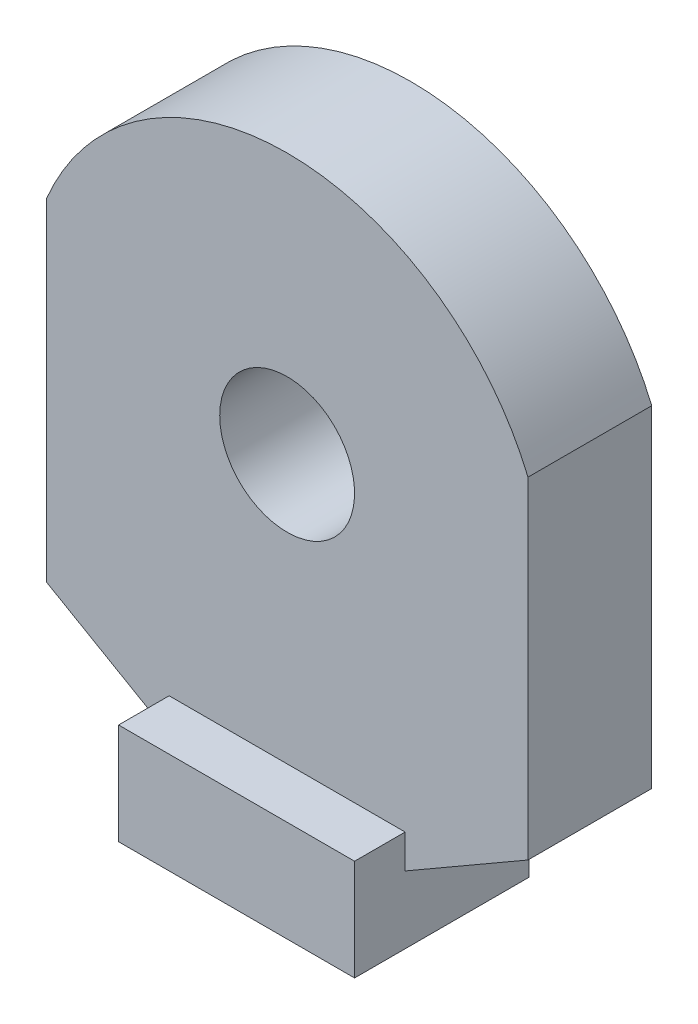
SolidWorks part; units mm, degrees
ref_plane "Plan de face" through (0, 0, 0) normal (0, 0, 1) x (1, 0, 0)
ref_plane "Plan de dessus" through (0, 0, 0) normal (0, 1, 0) x (1, 0, 0)
ref_plane "Plan de droite" through (0, 0, 0) normal (1, 0, 0) x (0, 0, -1)
sketch "Esquisse1" plane through (0, 0, 0) normal (0, 0, 1) x (1, 0, 0)
  line L0 (-14.29, -13.6911) -> (-14.29, 5.978)
  line L1 (-14.29, -13.6911) -> (-7, -17.9)
  line L2 (-7, -17.9) -> (-7, -21.9)
  line L3 (0, -21.9) -> (0, 14.503) construction
  line L4 (-7, -21.9) -> (7, -21.9)
  line L5 (7, -17.9) -> (7, -21.9)
  line L6 (14.29, -13.6911) -> (7, -17.9)
  line L7 (14.29, -13.6911) -> (14.29, 5.978)
  circle A0 centre (0, 0) radius 4
  arc A1 (-14.29, 5.978) -> (14.29, 5.978) centre (0, 0) cw
  point P13 (0, 15.49)
  dimension "D1" = 15.49
  dimension "D4" = 4
  dimension "D2" = 37.39
  dimension "D3" = 14.29
  dimension "D5" = 7
  dimension "D6" = 4
  dimension "D7" = 120
extrude "Boss.-Extru.1" add sketch "Esquisse1" along normal blind 7.34
sketch "Esquisse2" plane through (0, 0, 7.34) normal (0, 0, 1) x (1, 0, 0)
  line L0 (7, -21.9) -> (7, -17.9) construction
  line L1 (-7, -21.9) -> (7, -21.9)
  line L2 (-7, -21.9) -> (-7, -15.9)
  line L3 (-7, -15.9) -> (7, -15.9)
  line L4 (7, -21.9) -> (7, -15.9)
  dimension "D1" = 6
extrude "Boss.-Extru.2" add sketch "Esquisse2" along normal blind 3
